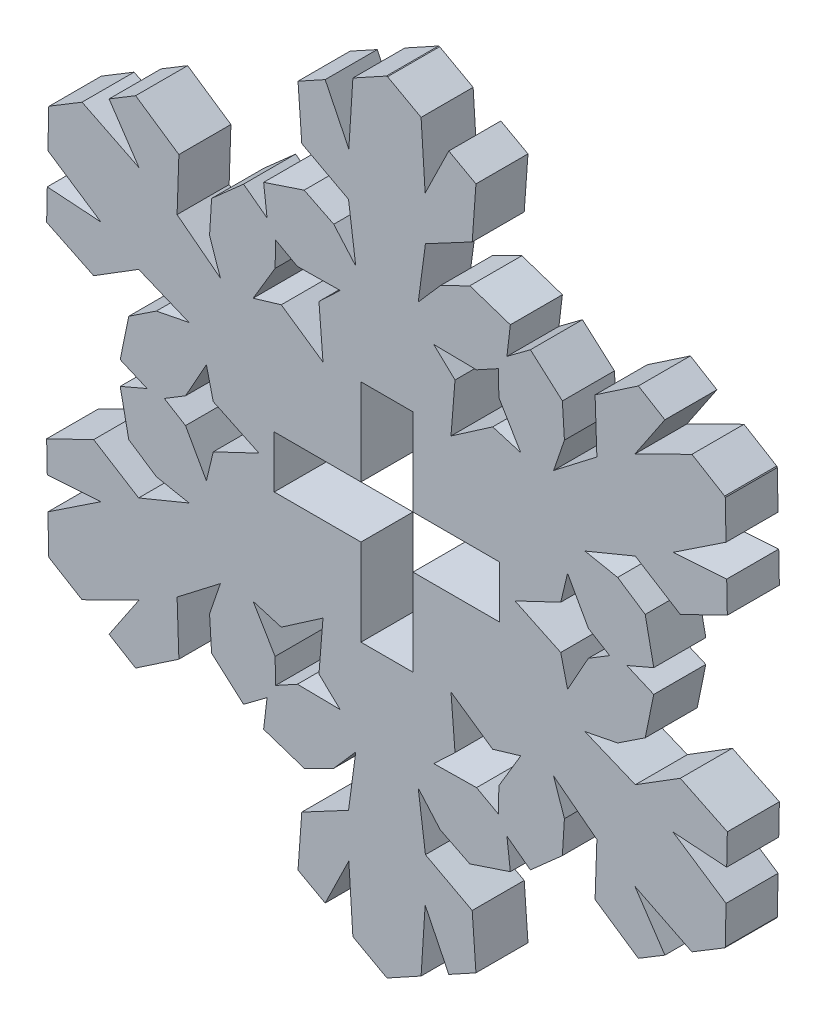
SolidWorks part; units mm, degrees
ref_plane "Спереди" through (0, 0, 0) normal (0, 0, 1) x (1, 0, 0)
ref_plane "Сверху" through (0, 0, 0) normal (0, 1, 0) x (1, 0, 0)
ref_plane "Справа" through (0, 0, 0) normal (1, 0, 0) x (0, 0, -1)
sketch "Model" plane through (0, 0, 0) normal (0, 0, 1) x (1, 0, 0)
  line L0 (0, 45) -> (1.932, 43.9368)
  line L1 (1.932, 43.9368) -> (2.1657, 40.274)
  line L2 (2.1657, 40.274) -> (3.5293, 43.0577)
  line L3 (3.5293, 43.0577) -> (5.095, 42.1961)
  line L4 (5.095, 42.1961) -> (4.8781, 39.1897)
  line L5 (4.8781, 39.1897) -> (2.1828, 37.7532)
  line L6 (2.1828, 37.7532) -> (1.768, 34.6339)
  line L7 (1.768, 34.6339) -> (3.0349, 36.0833)
  line L8 (3.0349, 36.0833) -> (4.741, 36.9329)
  line L9 (4.741, 36.9329) -> (7.0776, 36.1545)
  line L10 (7.0776, 36.1545) -> (6.8807, 34.477)
  line L11 (6.8807, 34.477) -> (8.2351, 35.4863)
  line L12 (8.2351, 35.4863) -> (10.0775, 33.8519)
  line L13 (10.0775, 33.8519) -> (10.1947, 31.9495)
  line L14 (10.1947, 31.9495) -> (9.573, 30.1277)
  line L15 (9.573, 30.1277) -> (12.067, 32.0465)
  line L16 (12.067, 32.0465) -> (11.9634, 35.099)
  line L17 (11.9634, 35.099) -> (14.4585, 36.79)
  line L18 (14.4585, 36.79) -> (15.9876, 35.8649)
  line L19 (15.9876, 35.8649) -> (14.2586, 33.2921)
  line L20 (14.2586, 33.2921) -> (17.5475, 34.9212)
  line L21 (17.5475, 34.9212) -> (19.4343, 33.7796)
  line L22 (19.4343, 33.7796) -> (19.4685, 33.7204)
  line L23 (19.4685, 33.7204) -> (19.5137, 31.5156)
  line L24 (19.5137, 31.5156) -> (16.4584, 29.4818)
  line L25 (16.4584, 29.4818) -> (19.5511, 29.6928)
  line L26 (19.5511, 29.6928) -> (19.5877, 27.906)
  line L27 (19.5877, 27.906) -> (16.8757, 26.5907)
  line L28 (16.8757, 26.5907) -> (14.284, 28.2067)
  line L29 (14.284, 28.2067) -> (11.3752, 27.0062)
  line L30 (11.3752, 27.0062) -> (13.2638, 26.6337)
  line L31 (13.2638, 26.6337) -> (14.8527, 25.5811)
  line L32 (14.8527, 25.5811) -> (15.3469, 23.1682)
  line L33 (15.3469, 23.1682) -> (13.7956, 22.5)
  line L34 (13.7956, 22.5) -> (15.3469, 21.8318)
  line L35 (15.3469, 21.8318) -> (14.8527, 19.4189)
  line L36 (14.8527, 19.4189) -> (13.2637, 18.3662)
  line L37 (13.2637, 18.3662) -> (11.3752, 17.9938)
  line L38 (11.3752, 17.9938) -> (14.284, 16.7933)
  line L39 (14.284, 16.7933) -> (16.8757, 18.4093)
  line L40 (16.8757, 18.4093) -> (19.5877, 17.094)
  line L41 (19.5877, 17.094) -> (19.5511, 15.3072)
  line L42 (19.5511, 15.3072) -> (16.4584, 15.5182)
  line L43 (16.4584, 15.5182) -> (19.5137, 13.4844)
  line L44 (19.5137, 13.4844) -> (19.4685, 11.2796)
  line L45 (19.4685, 11.2796) -> (19.4343, 11.2204)
  line L46 (19.4343, 11.2204) -> (17.5475, 10.0788)
  line L47 (17.5475, 10.0788) -> (14.2586, 11.7079)
  line L48 (14.2586, 11.7079) -> (15.9876, 9.1351)
  line L49 (15.9876, 9.1351) -> (14.4585, 8.21)
  line L50 (14.4585, 8.21) -> (11.9634, 9.901)
  line L51 (11.9634, 9.901) -> (12.067, 12.9534)
  line L52 (12.067, 12.9534) -> (9.5729, 14.8723)
  line L53 (9.5729, 14.8723) -> (10.1947, 13.0505)
  line L54 (10.1947, 13.0505) -> (10.0775, 11.1481)
  line L55 (10.0775, 11.1481) -> (8.2351, 9.5137)
  line L56 (8.2351, 9.5137) -> (6.8807, 10.523)
  line L57 (6.8807, 10.523) -> (7.0776, 8.8455)
  line L58 (7.0776, 8.8455) -> (4.741, 8.0671)
  line L59 (4.741, 8.0671) -> (3.0348, 8.9168)
  line L60 (3.0348, 8.9168) -> (1.768, 10.3661)
  line L61 (1.768, 10.3661) -> (2.1828, 7.2468)
  line L62 (2.1828, 7.2468) -> (4.8781, 5.8103)
  line L63 (4.8781, 5.8103) -> (5.095, 2.8039)
  line L64 (5.095, 2.8039) -> (3.5293, 1.9422)
  line L65 (3.5293, 1.9422) -> (2.1657, 4.726)
  line L66 (2.1657, 4.726) -> (1.932, 1.0632)
  line L67 (1.932, 1.0632) -> (0, 0)
  line L68 (0, 0) -> (-0.0684, 0)
  line L69 (-0.0684, 0) -> (-2.0003, 1.0632)
  line L70 (-2.0003, 1.0632) -> (-2.2341, 4.726)
  line L71 (-2.2341, 4.726) -> (-3.5977, 1.9423)
  line L72 (-3.5977, 1.9423) -> (-5.1634, 2.8039)
  line L73 (-5.1634, 2.8039) -> (-4.9465, 5.8103)
  line L74 (-4.9465, 5.8103) -> (-2.2512, 7.2468)
  line L75 (-2.2512, 7.2468) -> (-1.8364, 10.3661)
  line L76 (-1.8364, 10.3661) -> (-3.1033, 8.9167)
  line L77 (-3.1033, 8.9167) -> (-4.8093, 8.0671)
  line L78 (-4.8093, 8.0671) -> (-7.146, 8.8455)
  line L79 (-7.146, 8.8455) -> (-6.9491, 10.523)
  line L80 (-6.9491, 10.523) -> (-8.3034, 9.5137)
  line L81 (-8.3034, 9.5137) -> (-10.1459, 11.1481)
  line L82 (-10.1459, 11.1481) -> (-10.2631, 13.0505)
  line L83 (-10.2631, 13.0505) -> (-9.6414, 14.8723)
  line L84 (-9.6414, 14.8723) -> (-12.1354, 12.9534)
  line L85 (-12.1354, 12.9534) -> (-12.0318, 9.901)
  line L86 (-12.0318, 9.901) -> (-14.5269, 8.21)
  line L87 (-14.5269, 8.21) -> (-16.056, 9.1351)
  line L88 (-16.056, 9.1351) -> (-14.327, 11.7079)
  line L89 (-14.327, 11.7079) -> (-17.6159, 10.0788)
  line L90 (-17.6159, 10.0788) -> (-19.5027, 11.2204)
  line L91 (-19.5027, 11.2204) -> (-19.5369, 11.2796)
  line L92 (-19.5369, 11.2796) -> (-19.5821, 13.4844)
  line L93 (-19.5821, 13.4844) -> (-16.5268, 15.5182)
  line L94 (-16.5268, 15.5182) -> (-19.6194, 15.3072)
  line L95 (-19.6194, 15.3072) -> (-19.6561, 17.094)
  line L96 (-19.6561, 17.094) -> (-16.944, 18.4093)
  line L97 (-16.944, 18.4093) -> (-14.3524, 16.7933)
  line L98 (-14.3524, 16.7933) -> (-11.4436, 17.9938)
  line L99 (-11.4436, 17.9938) -> (-13.3322, 18.3663)
  line L100 (-13.3322, 18.3663) -> (-14.9211, 19.4189)
  line L101 (-14.9211, 19.4189) -> (-15.4153, 21.8318)
  line L102 (-15.4153, 21.8318) -> (-13.864, 22.5)
  line L103 (-13.864, 22.5) -> (-15.4153, 23.1682)
  line L104 (-15.4153, 23.1682) -> (-14.9211, 25.5811)
  line L105 (-14.9211, 25.5811) -> (-13.3321, 26.6338)
  line L106 (-13.3321, 26.6338) -> (-11.4436, 27.0062)
  line L107 (-11.4436, 27.0062) -> (-14.3524, 28.2067)
  line L108 (-14.3524, 28.2067) -> (-16.944, 26.5907)
  line L109 (-16.944, 26.5907) -> (-19.6561, 27.906)
  line L110 (-19.6561, 27.906) -> (-19.6195, 29.6928)
  line L111 (-19.6195, 29.6928) -> (-16.5268, 29.4818)
  line L112 (-16.5268, 29.4818) -> (-19.5821, 31.5156)
  line L113 (-19.5821, 31.5156) -> (-19.5369, 33.7204)
  line L114 (-19.5369, 33.7204) -> (-19.5027, 33.7796)
  line L115 (-19.5027, 33.7796) -> (-17.6159, 34.9212)
  line L116 (-17.6159, 34.9212) -> (-14.327, 33.2921)
  line L117 (-14.327, 33.2921) -> (-16.0559, 35.8649)
  line L118 (-16.0559, 35.8649) -> (-14.5269, 36.79)
  line L119 (-14.5269, 36.79) -> (-12.0318, 35.099)
  line L120 (-12.0318, 35.099) -> (-12.1354, 32.0465)
  line L121 (-12.1354, 32.0465) -> (-9.6413, 30.1277)
  line L122 (-9.6413, 30.1277) -> (-10.2631, 31.9495)
  line L123 (-10.2631, 31.9495) -> (-10.1459, 33.8519)
  line L124 (-10.1459, 33.8519) -> (-8.3034, 35.4863)
  line L125 (-8.3034, 35.4863) -> (-6.9491, 34.477)
  line L126 (-6.9491, 34.477) -> (-7.146, 36.1545)
  line L127 (-7.146, 36.1545) -> (-4.8093, 36.9329)
  line L128 (-4.8093, 36.9329) -> (-3.1032, 36.0832)
  line L129 (-3.1032, 36.0832) -> (-1.8364, 34.6339)
  line L130 (-1.8364, 34.6339) -> (-2.2512, 37.7532)
  line L131 (-2.2512, 37.7532) -> (-4.9465, 39.1897)
  line L132 (-4.9465, 39.1897) -> (-5.1634, 42.1961)
  line L133 (-5.1634, 42.1961) -> (-3.5977, 43.0577)
  line L134 (-3.5977, 43.0577) -> (-2.2341, 40.274)
  line L135 (-2.2341, 40.274) -> (-2.0003, 43.9368)
  line L136 (-2.0003, 43.9368) -> (-0.0684, 45)
  line L137 (-0.0684, 45) -> (0, 45)
  line L138 (6.385, 33.6184) -> (5.1294, 32.9309)
  line L139 (5.1294, 32.9309) -> (2.6621, 32.9644)
  line L140 (2.6621, 32.9644) -> (3.8879, 31.8023)
  line L141 (3.8879, 31.8023) -> (3.6555, 28.8908)
  line L142 (3.6555, 28.8908) -> (6.0609, 30.5478)
  line L143 (6.0609, 30.5478) -> (7.6801, 30.0673)
  line L144 (7.6801, 30.0673) -> (6.4174, 32.1872)
  line L145 (6.4174, 32.1872) -> (6.385, 33.6184)
  line L146 (1.4658, 16) -> (1.4658, 21)
  line L147 (1.4658, 21) -> (6.4658, 21)
  line L148 (6.4658, 21) -> (6.4658, 24)
  line L149 (6.4658, 24) -> (1.4658, 24)
  line L150 (1.4658, 24) -> (1.4658, 29)
  line L151 (1.4658, 29) -> (-1.5342, 29)
  line L152 (-1.5342, 29) -> (-1.5342, 24)
  line L153 (-1.5342, 24) -> (-6.5342, 24)
  line L154 (-6.5342, 24) -> (-6.5342, 21)
  line L155 (-6.5342, 21) -> (-1.5342, 21)
  line L156 (-1.5342, 21) -> (-1.5342, 16)
  line L157 (-1.5342, 16) -> (1.4658, 16)
  line L158 (-12.8726, 22.5) -> (-11.6494, 21.7564)
  line L159 (-11.6494, 21.7564) -> (-10.4448, 19.6029)
  line L160 (-10.4448, 19.6029) -> (-10.0513, 21.2454)
  line L161 (-10.0513, 21.2454) -> (-7.4136, 22.5)
  line L162 (-7.4136, 22.5) -> (-10.0513, 23.7546)
  line L163 (-10.0513, 23.7546) -> (-10.4448, 25.3971)
  line L164 (-10.4448, 25.3971) -> (-11.6494, 23.2436)
  line L165 (-11.6494, 23.2436) -> (-12.8726, 22.5)
  line L166 (-3.7239, 28.8908) -> (-3.9562, 31.8024)
  line L167 (-3.9562, 31.8024) -> (-2.7305, 32.9644)
  line L168 (-2.7305, 32.9644) -> (-5.1978, 32.9309)
  line L169 (-5.1978, 32.9309) -> (-6.4534, 33.6184)
  line L170 (-6.4534, 33.6184) -> (-6.4858, 32.1872)
  line L171 (-6.4858, 32.1872) -> (-7.7485, 30.0673)
  line L172 (-7.7485, 30.0673) -> (-6.1292, 30.5478)
  line L173 (-6.1292, 30.5478) -> (-3.7239, 28.8908)
  line L174 (12.8042, 22.5) -> (11.581, 23.2436)
  line L175 (11.581, 23.2436) -> (10.3764, 25.3971)
  line L176 (10.3764, 25.3971) -> (9.9829, 23.7546)
  line L177 (9.9829, 23.7546) -> (7.3452, 22.5)
  line L178 (7.3452, 22.5) -> (9.9829, 21.2454)
  line L179 (9.9829, 21.2454) -> (10.3764, 19.6029)
  line L180 (10.3764, 19.6029) -> (11.581, 21.7564)
  line L181 (11.581, 21.7564) -> (12.8042, 22.5)
  line L182 (6.385, 11.3816) -> (6.4174, 12.8128)
  line L183 (6.4174, 12.8128) -> (7.6801, 14.9327)
  line L184 (7.6801, 14.9327) -> (6.0608, 14.4522)
  line L185 (6.0608, 14.4522) -> (3.6555, 16.1092)
  line L186 (3.6555, 16.1092) -> (3.8878, 13.1976)
  line L187 (3.8878, 13.1976) -> (2.6621, 12.0356)
  line L188 (2.6621, 12.0356) -> (5.1294, 12.0691)
  line L189 (5.1294, 12.0691) -> (6.385, 11.3816)
  line L190 (-6.4534, 11.3816) -> (-5.1978, 12.0691)
  line L191 (-5.1978, 12.0691) -> (-2.7305, 12.0356)
  line L192 (-2.7305, 12.0356) -> (-3.9563, 13.1977)
  line L193 (-3.9563, 13.1977) -> (-3.7239, 16.1092)
  line L194 (-3.7239, 16.1092) -> (-6.1292, 14.4522)
  line L195 (-6.1292, 14.4522) -> (-7.7485, 14.9327)
  line L196 (-7.7485, 14.9327) -> (-6.4858, 12.8128)
  line L197 (-6.4858, 12.8128) -> (-6.4534, 11.3816)
extrude "Бобышка-Вытянуть1" add sketch "Model" along normal blind 3
